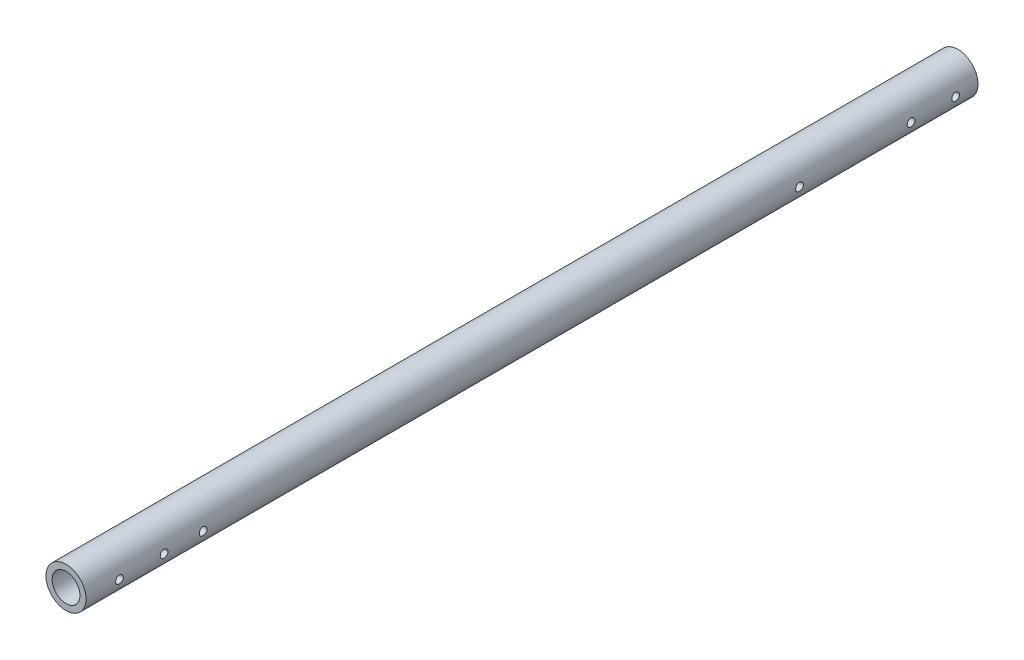
SolidWorks part; units mm, degrees
material "ﾎﾟﾘ塩化ﾋﾞﾆﾙ(PVC)硬質"
ref_plane "正面(Front)" through (0, 0, 0) normal (0, 0, 1) x (1, 0, 0)
ref_plane "平面(Top)" through (0, 0, 0) normal (0, 1, 0) x (1, 0, 0)
ref_plane "右側面(Right)" through (0, 0, 0) normal (1, 0, 0) x (0, 0, -1)
sketch "ｽｹｯﾁ1" plane through (0, 0, 0) normal (0, 0, 1) x (1, 0, 0)
  circle A0 centre (0, 0) radius 9
  circle A1 centre (0, 0) radius 6.25
  dimension "D1" = 18
  dimension "D2" = 12.5
extrude "ﾎﾞｽ - 押し出し1" add sketch "ｽｹｯﾁ1" along normal blind 400
sketch "ｽｹｯﾁ2" plane through (0, 0, 0) normal (1, 0, 0) x (0, 0, -1)
  line L0 (0, 0) -> (-400, 0) construction
  line L1 (0, -9) -> (0, 9) construction
  line L2 (-400, 9) -> (-400, -9) construction
  line L3 (-200, 0) -> (-200, 72.1876) construction
  circle A0 centre (-10, 0) radius 1.75
  circle A1 centre (-385, 0) radius 1.75
  circle A2 centre (-30, 0) radius 1.75
  circle A3 centre (-365, 0) radius 1.75
  circle A4 centre (-347.5, 0) radius 1.75
  circle A5 centre (-80, 0) radius 1.75
  dimension "D2" = 15
  dimension "D3" = 3.5
  dimension "D4" = 20
  dimension "D5" = 20
  dimension "D6" = 17.5
  dimension "D7" = 50
  dimension "D1" = 10
extrude "ｶｯﾄ - 押し出し1" cut sketch "ｽｹｯﾁ2" against normal through all both and the other way through all
